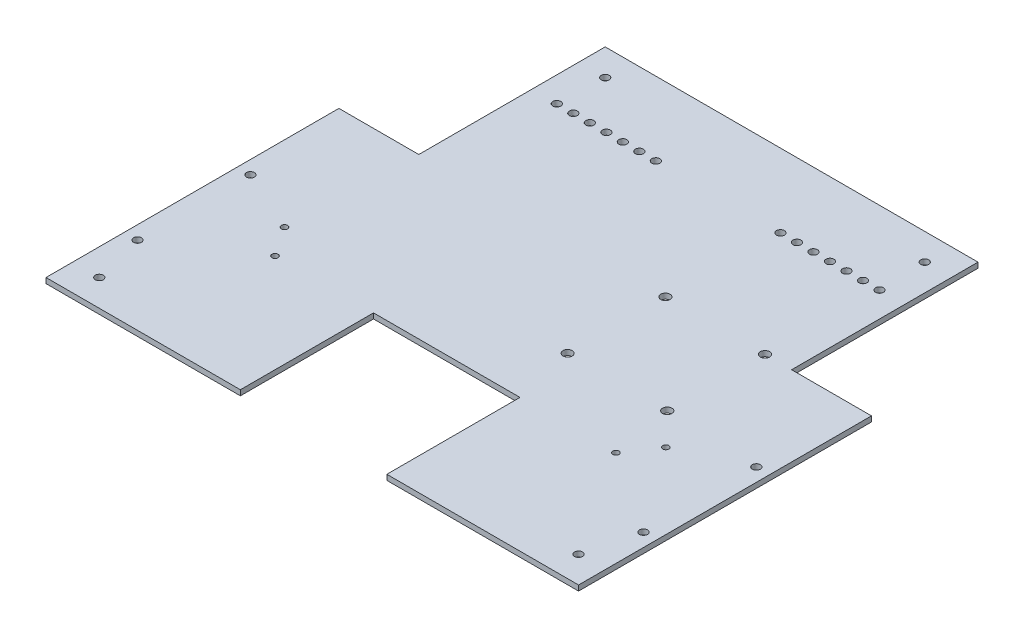
SolidWorks part; units mm, degrees
ref_plane "Front Plane" through (0, 0, 0) normal (0, 0, 1) x (1, 0, 0)
ref_plane "Top Plane" through (0, 0, 0) normal (0, 1, 0) x (1, 0, 0)
ref_plane "Right Plane" through (0, 0, 0) normal (1, 0, 0) x (0, 0, -1)
sketch "Sketch1" plane through (0, 0, 0) normal (0, 1, 0) x (1, 0, 0)
  line L1 (-100, -90) -> (100, -90)
  line L2 (-100, -90) -> (-100, 90)
  line L3 (-100, 90) -> (100, 90)
  line L4 (100, -90) -> (100, 90)
  line L5 (-100, -90) -> (100, 90) construction
  line L6 (-100, 90) -> (100, -90) construction
  point P0 (0, 0)
  dimension "D1" = 180
  dimension "D2" = 200
extrude "Boss-Extrude1" add sketch "Sketch1" along normal blind 2
sketch "Sketch2" plane through (0, 2, 0) normal (0, 1, 0) x (1, 0, 0)
  line L0 (-100, -90) -> (100, -90) construction
  line L5 (-27, -90) -> (28, -90)
  line L6 (-27, -90) -> (-27, -40)
  line L7 (-27, -40) -> (28, -40)
  line L8 (28, -90) -> (28, -40)
  line L9 (-100, 90) -> (-100, -90) construction
  line L10 (100, -90) -> (100, 90) construction
  dimension "D1" = 50
  dimension "D2" = 55
  dimension "D3" = 73
  dimension "D4" = 72
extrude "Cut-Extrude1" cut sketch "Sketch2" against normal blind 4
sketch "Sketch3" plane through (0, 2, 0) normal (0, 1, 0) x (1, 0, 0)
  line L0 (0, 0) -> (0, 112.6395) construction
  line L1 (100, 90) -> (70, 90)
  line L2 (100, 90) -> (100, 20)
  line L3 (100, 20) -> (70, 20)
  line L4 (70, 90) -> (70, 20)
  line L5 (-100, 90) -> (-70, 90)
  line L6 (-100, 90) -> (-100, 20)
  line L7 (-100, 20) -> (-70, 20)
  line L8 (-70, 90) -> (-70, 20)
  dimension "D1" = 70
  dimension "D2" = 30
extrude "Cut-Extrude2" cut sketch "Sketch3" against normal blind 16
sketch "Sketch4" plane through (0, 2, 0) normal (0, 1, 0) x (1, 0, 0)
  line L0 (100, -90) -> (100, 20) construction
  line L1 (28, -90) -> (100, -90) construction
  line L2 (-100, -90) -> (-27, -90) construction
  line L3 (-100, 20) -> (-100, -90) construction
  line L4 (70, 90) -> (-70, 90) construction
  line L5 (-70, 20) -> (-70, 90) construction
  line L6 (70, 90) -> (70, 20) construction
  circle A0 centre (90, -80) radius 1.5
  circle A1 centre (-90, -80) radius 1.5
  circle A2 centre (60, 80) radius 1.5
  circle A3 centre (-60, 80) radius 1.5
  dimension "D1" = 3
  dimension "D2" = 3
  dimension "D3" = 3
  dimension "D4" = 3
  dimension "D5" = 10
  dimension "D6" = 10
  dimension "D7" = 10
  dimension "D8" = 10
  dimension "D9" = 10
  dimension "D10" = 10
  dimension "D11" = 10
  dimension "D12" = 10
extrude "Cut-Extrude3" cut sketch "Sketch4" against normal blind 10
sketch "Sketch5" plane through (0, 2, 0) normal (0, 1, 0) x (1, 0, 0)
  line L0 (70, 90) -> (-70, 90) construction
  line L1 (70, 90) -> (70, 20) construction
  circle A0 centre (60, 20) radius 1.75
  circle A1 centre (22.6, 20) radius 1.75
  circle A2 centre (22.6, -16.7) radius 1.75
  circle A3 centre (60, -16.7) radius 1.75
  dimension "D1" = 3.5
  dimension "D4" = 3.5
  dimension "D6" = 3.5
  dimension "D7" = 3.5
  dimension "D2" = 70
  dimension "D3" = 10
  dimension "D5" = 37.4
  dimension "D8" = 36.7
  dimension "D9" = 36.7
extrude "Cut-Extrude4" cut sketch "Sketch5" against normal blind 10
sketch "Sketch6" plane through (0, 2, 0) normal (0, 1, 0) x (1, 0, 0)
  line L0 (-100, 20) -> (-100, -90) construction
  line L1 (0, 0) -> (0, -40) construction
  line L2 (28, -40) -> (-27, -40) construction
  circle A0 centre (-95, -60.6351) radius 1.5
  circle A1 centre (-90, -80) radius 1.5 construction
  circle A2 centre (-95, -18.2351) radius 1.5
  circle A3 centre (95, -60.6351) radius 1.5
  circle A4 centre (95, -18.2351) radius 1.5
  dimension "D1" = 3
  dimension "D4" = 3
  dimension "D2" = 20
  dimension "D3" = 5
  dimension "D5" = 42.4
extrude "Cut-Extrude5" cut sketch "Sketch6" against normal blind 2
sketch "Sketch7" plane through (0, 0, 0) normal (0, -1, 0) x (1, 0, 0)
  line L0 (28, 40) -> (100, 40) construction
  line L1 (100, 90) -> (100, -20) construction
  line L2 (0, 0) -> (0, 40) construction
  line L3 (-27, 40) -> (28, 40) construction
  circle A0 centre (64, 40) radius 1.15
  circle A1 centre (71.5977, 28.8409) radius 1.15
  circle A2 centre (-64, 40) radius 1.15
  circle A3 centre (-71.5977, 28.8409) radius 1.15
  dimension "D1" = 2.3
  dimension "D2" = 2.3
  dimension "D3" = 13.5
extrude "Cut-Extrude6" cut sketch "Sketch7" against normal blind 2
sketch "Sketch8" plane through (0, 0, 0) normal (0, -1, 0) x (1, 0, 0)
  line L0 (70, -20) -> (70, -90) construction
  line L1 (70, -90) -> (-70, -90) construction
  line L2 (0, 0) -> (0, -90) construction
  circle A0 centre (60.59, -62.42) radius 1.5
  circle A1 centre (54.39, -62.42) radius 1.5
  circle A2 centre (48.19, -62.42) radius 1.5
  circle A3 centre (41.99, -62.42) radius 1.5
  circle A4 centre (35.79, -62.42) radius 1.5
  circle A5 centre (29.59, -62.42) radius 1.5
  circle A6 centre (23.39, -62.42) radius 1.5
  circle A7 centre (-23.39, -62.42) radius 1.5
  circle A8 centre (-29.59, -62.42) radius 1.5
  circle A9 centre (-35.79, -62.42) radius 1.5
  circle A10 centre (-41.99, -62.42) radius 1.5
  circle A11 centre (-60.59, -62.42) radius 1.5
  circle A12 centre (-54.39, -62.42) radius 1.5
  circle A13 centre (-48.19, -62.42) radius 1.5
  dimension "D1" = 3
  dimension "D2" = 9.41
  dimension "D3" = 27.58
  dimension "D4" = 7
extrude "Cut-Extrude7" cut sketch "Sketch8" against normal blind 2
